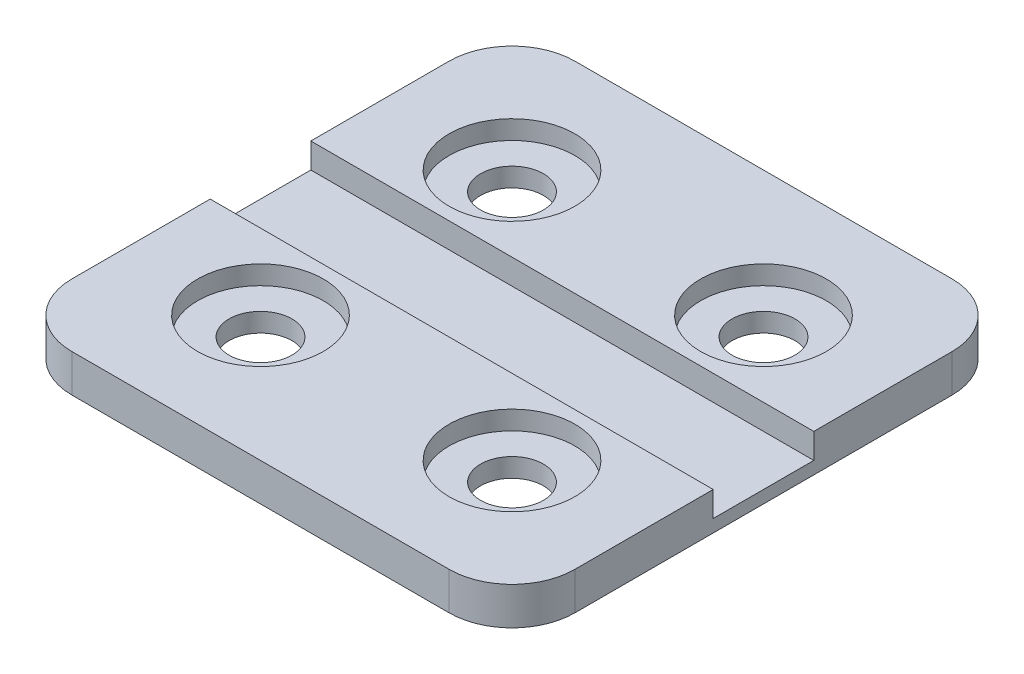
SolidWorks part; units mm, degrees
ref_plane "Front Plane" through (0, 0, 0) normal (0, 0, 1) x (1, 0, 0)
ref_plane "Top Plane" through (0, 0, 0) normal (0, 1, 0) x (1, 0, 0)
ref_plane "Right Plane" through (0, 0, 0) normal (1, 0, 0) x (0, 0, -1)
sketch "Sketch1" plane through (0, 0, 0) normal (0, 1, 0) x (1, 0, 0)
  line L1 (-20, -20) -> (20, -20)
  line L2 (-20, -20) -> (-20, 20)
  line L3 (-20, 20) -> (20, 20)
  line L4 (20, -20) -> (20, 20)
  line L5 (0, 20) -> (0, -20) construction
  line L6 (-20, 0) -> (20, 0) construction
  point P0 (0, 0)
  dimension "D1" = 40
  dimension "D2" = 40
extrude "Boss-Extrude1" add sketch "Sketch1" along normal blind 3
sketch "Sketch2" plane through (0, 3, 0) normal (0, 1, 0) x (1, 0, 0)
  line L1 (-10, -10) -> (10, -10)
  line L2 (-10, -10) -> (-10, 10)
  line L3 (-10, 10) -> (10, 10)
  line L4 (10, -10) -> (10, 10)
  line L5 (0, 10) -> (0, -10) construction
  line L6 (-10, 0) -> (10, 0) construction
  circle A0 centre (-10, 10) radius 5
  circle A1 centre (10, 10) radius 5
  circle A2 centre (-10, -10) radius 5
  circle A3 centre (10, -10) radius 5
  point P0 (0, 0)
  dimension "D3" = 10
  dimension "D1" = 20
  dimension "D2" = 20
extrude "Cut-Extrude1" cut sketch "Sketch2" against normal blind 1.5 contours L3 A0 L2 | L2 A0 L3 | L4 A1 L3 | L3 A1 L4 | L2 A2 L1 | L1 A2 L2 | L1 A3 L4 | L4 A3 L1
sketch "Sketch3" plane through (0, 1.5, 0) normal (0, 1, 0) x (1, 0, 0)
  circle A0 centre (-10, 10) radius 2.5
  circle A1 centre (10, 10) radius 2.5
  circle A2 centre (-10, -10) radius 2.5
  circle A3 centre (10, -10) radius 2.5
  dimension "D1" = 5
extrude "Cut-Extrude2" cut sketch "Sketch3" against normal through all
fillet "Fillet1" radius 5 4 edges at (-20, 1.5, 20) (20, 1.5, 20) (20, 1.5, -20) (-20, 1.5, -20)
sketch "Sketch4" plane through (0, 3, 0) normal (0, 1, 0) x (1, 0, 0)
  line L0 (-20, 15) -> (-20, -15) construction
  line L1 (-20, 4) -> (20, 4)
  line L2 (-20, 4) -> (-20, -4)
  line L3 (-20, -4) -> (20, -4)
  line L4 (20, 4) -> (20, -4)
  line L5 (20, -15) -> (20, 15) construction
  point P8 (-20, 0)
  dimension "D1" = 8
extrude "Cut-Extrude3" cut sketch "Sketch4" against normal offset from surface (2 mm away) 1 up to face at (10, 0, -7.5)
